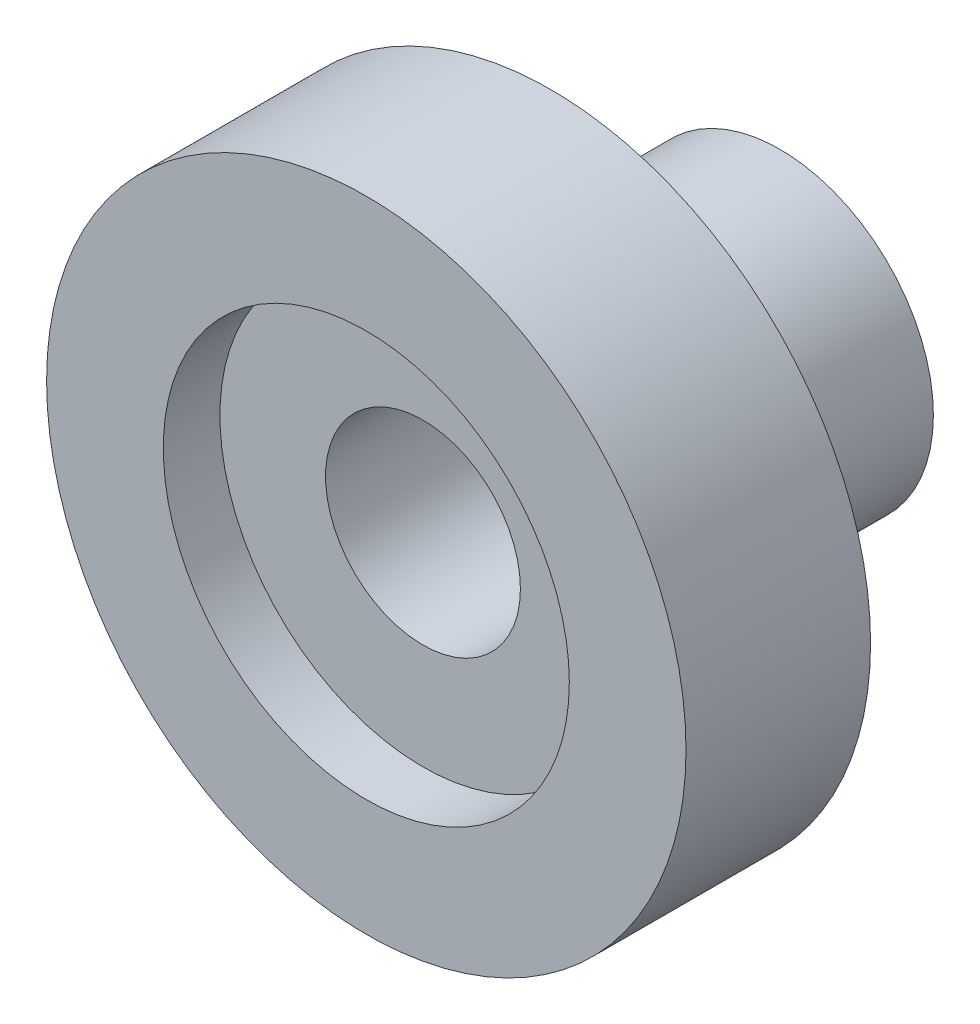
SolidWorks part; units mm, degrees
ref_plane "Front Plane" through (0, 0, 0) normal (0, 0, 1) x (1, 0, 0)
ref_plane "Top Plane" through (0, 0, 0) normal (0, 1, 0) x (1, 0, 0)
ref_plane "Right Plane" through (0, 0, 0) normal (1, 0, 0) x (0, 0, -1)
sketch "Sketch1" plane through (0, 0, 0) normal (0, 0, 1) x (1, 0, 0)
  circle A0 centre (0, 0) radius 6
  circle A1 centre (0, 0) radius 3.81
  dimension "D1" = 12
  dimension "D2" = 7.62
extrude "Boss-Extrude1" add sketch "Sketch1" along normal blind 18.9352
sketch "Sketch2" plane through (0, 0, 18.9352) normal (0, 0, 1) x (1, 0, 0)
  circle A0 centre (0, 0) radius 8.3746
extrude "Cut-Extrude1" cut sketch "Sketch2" against normal blind 4.9784
sketch "Sketch3" plane through (0, 0, 13.9568) normal (0, 0, 1) x (1, 0, 0)
  circle A0 centre (0, 0) radius 7.9375
  circle A1 centre (0, 0) radius 12.5
  dimension "D1" = 15.875
  dimension "D2" = 25
extrude "Boss-Extrude2" add sketch "Sketch3" along normal blind 3.216 separate body
sketch "Sketch4" plane through (0, 0, 13.9568) normal (0, 0, -1) x (-1, 0, 0)
  circle A0 centre (0, 0) radius 6 construction
  circle A1 centre (0, 0) radius 12.5 construction
  circle A2 centre (0, 0) radius 6
  circle A3 centre (0, 0) radius 12.5
extrude "Boss-Extrude3" add sketch "Sketch4" along normal blind 5
sketch "Sketch6" plane through (0, 0, 17.1728) normal (0, 0, 1) x (1, 0, 0)
  circle A0 centre (0, 0) radius 16.2996
extrude "Cut-Extrude2" cut sketch "Sketch6" against normal blind 1
